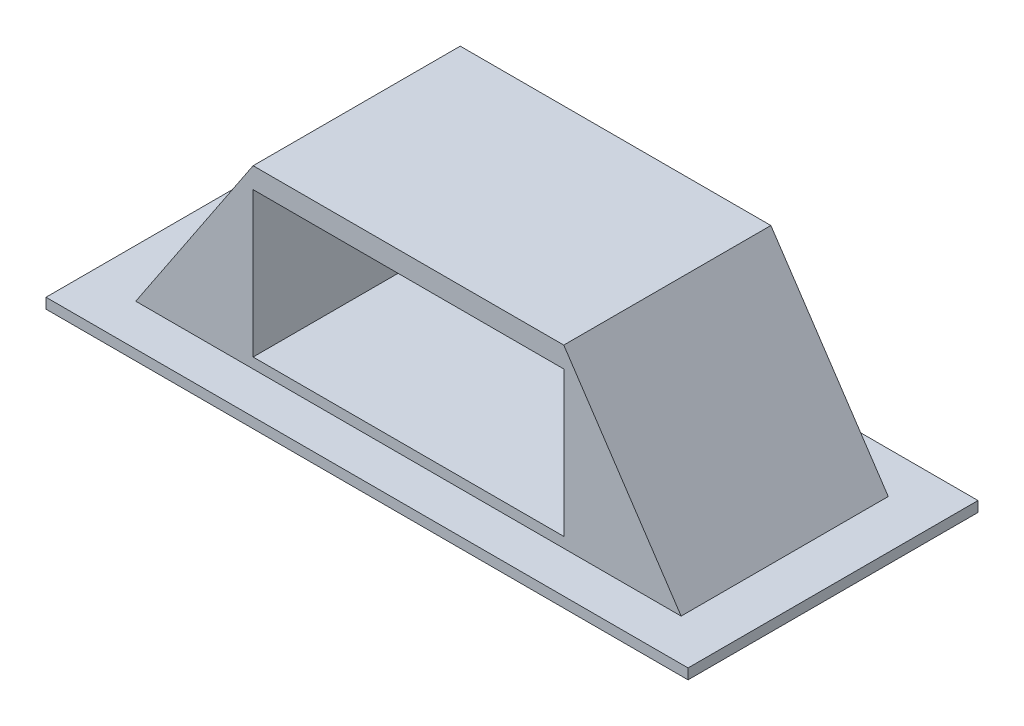
SolidWorks part; units mm, degrees
ref_plane "Front" through (0, 0, 0) normal (0, 0, 1) x (1, 0, 0)
ref_plane "Top" through (0, 0, 0) normal (0, 1, 0) x (1, 0, 0)
ref_plane "Right" through (0, 0, 0) normal (1, 0, 0) x (0, 0, -1)
sketch "草图2" plane through (0, 0, 0) normal (0, 1, 0) x (1, 0, 0)
  line L1 (-75, 50) -> (75, 50)
  line L2 (-75, 50) -> (-75, -50)
  line L3 (-75, -50) -> (75, -50)
  line L4 (75, 50) -> (75, -50)
  dimension "D1" = 75
  dimension "D2" = 75
  dimension "D3" = 50
  dimension "D4" = 50
extrude "凸台-拉伸1" add sketch "草图2" along normal blind 90
sketch "草图3" plane through (0, 0, 50) normal (0, 0, 1) x (1, 0, 0)
  line L0 (-75, 90) -> (75, 90) construction
  line L1 (-75, 80) -> (75, 80)
  line L2 (-75, 80) -> (-75, 10)
  line L3 (-75, 10) -> (75, 10)
  line L4 (75, 80) -> (75, 10)
  line L9 (-75, 90) -> (-75, 0) construction
  line L10 (75, 90) -> (75, 0) construction
  line L11 (-75, 89.4099) -> (-75, 90)
  point P14 (0, 0)
  point P15 (-123.1001, 0)
  point P16 (0, 0)
  line M11 (75, 0) -> (75, 90)
  line M13 (-75, 90) -> (-75, 0)
  dimension "D1" = 10
  dimension "D3" = 0
  dimension "D4" = 0
extrude "切除-拉伸1" cut sketch "草图3" against normal blind 80 contours L3 L1 M13 M11
sketch "草图5" plane through (0, 0, -50) normal (0, 0, -1) x (-1, 0, 0)
  line L0 (-75, 90) -> (-135, 0)
  line L1 (-75, 0) -> (-135, 0)
  line L2 (75, 0) -> (-75, 0) construction
  line L3 (-75, 0) -> (-75, 90)
extrude "凸台-拉伸2" add sketch "草图5" against normal blind 100
sketch "草图6" plane through (0, 0, -50) normal (0, 0, -1) x (-1, 0, 0)
  line L0 (75, 90) -> (135, 0)
  line L2 (75, 0) -> (-75, 0) construction
  line L3 (75, 0) -> (75, 90)
  line L4 (75, 0) -> (135, 0)
extrude "凸台-拉伸3" add sketch "草图6" against normal blind 100
sketch "草图7" plane through (0, 0, 0) normal (0, -1, 0) x (1, 0, 0)
  line L0 (-135, 50) -> (135, 50) construction
  line L1 (-155, 70) -> (155, 70)
  line L2 (-155, 70) -> (-155, -70)
  line L3 (-155, -70) -> (155, -70)
  line L4 (155, 70) -> (155, -70)
  line L5 (135, -50) -> (-135, -50) construction
  line L6 (-135, 50) -> (-135, -50) construction
  line L7 (135, 50) -> (135, -50) construction
  dimension "D1" = 20
  dimension "D2" = 20
  dimension "D3" = 20
  dimension "D4" = 20
extrude "凸台-拉伸4" add sketch "草图7" against normal blind 5
